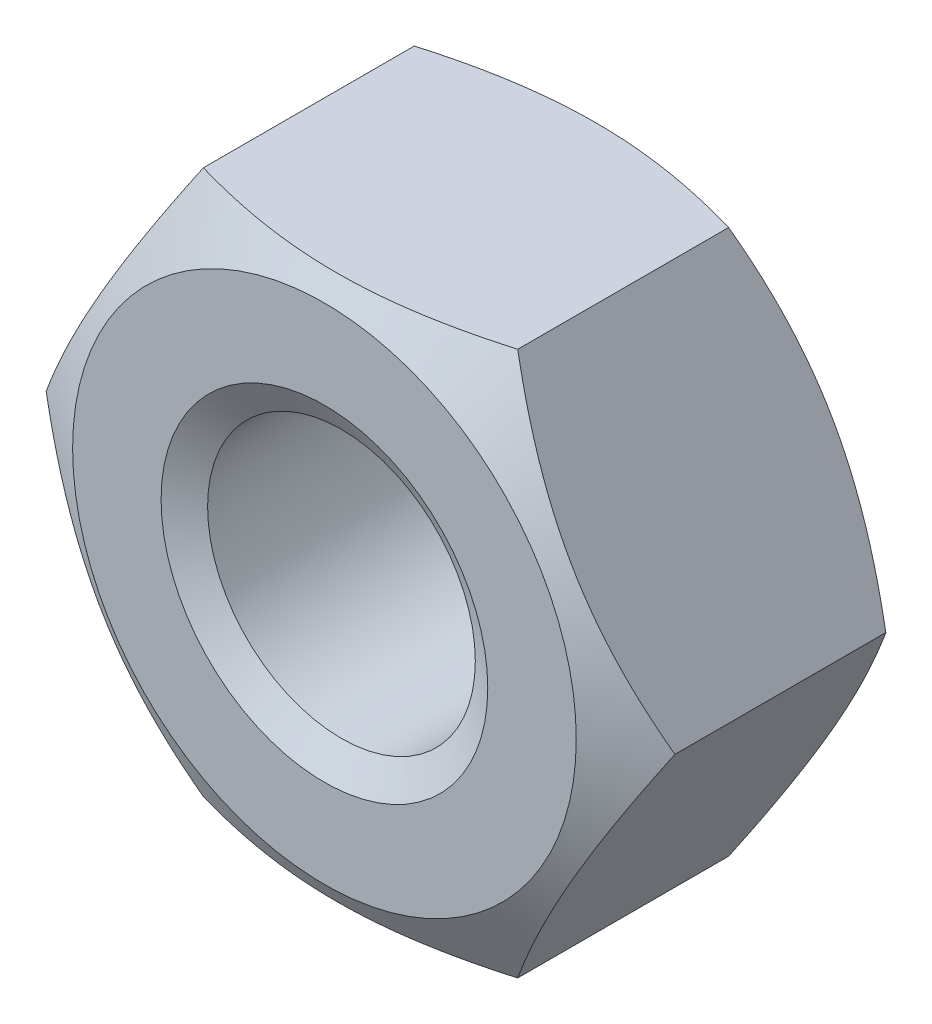
SolidWorks part; units mm, degrees
ref_plane "Front" through (0, 0, 0) normal (0, 0, 1) x (1, 0, 0)
ref_plane "Top" through (0, 0, 0) normal (0, 1, 0) x (1, 0, 0)
ref_plane "Right" through (0, 0, 0) normal (1, 0, 0) x (0, 0, -1)
sketch "Sketch1" plane through (0, 0, 0) normal (0, 0, 1) x (1, 0, 0)
  line L1 (5.7735, 0) -> (2.8868, 5)
  line L2 (2.8868, 5) -> (-2.8868, 5)
  line L3 (-2.8868, 5) -> (-5.7735, 0)
  line L4 (-5.7735, 0) -> (-2.8868, -5)
  line L5 (-2.8868, -5) -> (2.8868, -5)
  line L6 (2.8868, -5) -> (5.7735, 0)
  circle A0 centre (0, 0) radius 5 construction
  circle A1 centre (0, 0) radius 2.4585
  dimension "D" = 4.917
  dimension "s" = 10
extrude "BaseNut" add sketch "Sketch1" against normal blind 5.2
cosmetic thread "ThreadCosmetic1" [suppressed] parameters "D"=6
sketch "Sketch2" plane through (0, 0, 0) normal (0, 1, 0) x (1, 0, 0)
  line L0 (-5.7735, 5.2) -> (-4.625, 5.2)
  line L2 (-4.625, 5.2) -> (-5.7735, 4.5369)
  line L3 (-5.7735, 4.5369) -> (-5.7735, 5.2)
  line L4 (0, 3.3759) -> (0, -9.8171) construction
  line L6 (-9.7712, 2.6) -> (9.8853, 2.6) construction
  line L7 (-5.7735, 0.6631) -> (-5.7735, 0)
  line L8 (-4.625, 0) -> (-5.7735, 0.6631)
  line L9 (-5.7735, 0) -> (-4.625, 0)
  dimension "D1" = 30
  dimension "dw" = 9.25
  dimension "D2" = 2.6
revolve "Double-Chamfer" cut sketch "Sketch2" angle 360 about L4
chamfer "EndChamfer" distance 0.5415 angle 30 2 edges at (2.4585, 0, -5.2) (2.4585, 0, 0)
sketch "Sketch3" plane through (0, 0, 0) normal (0, 1, 0) x (1, 0, 0)
  line L0 (-2.9275, 4.6585) -> (-2.4585, 4.3877)
  line L1 (-2.4585, 4.3877) -> (-1.917, 4.3877)
  line L2 (-1.917, 4.3877) -> (-1.917, 4.9292)
  line L3 (-1.917, 4.9292) -> (-2.4585, 4.9292)
  line L4 (-2.4585, 4.9292) -> (-2.9275, 4.6585)
  line L5 (0, 7.4383) -> (0, 16.8806) construction
  dimension "D1" = 0.5415
  dimension "D2" = 4.917
revolve "Cut-Revolve10" [suppressed] cut sketch "Sketch3" angle 360 about L5
pattern_linear "LPattern10" [suppressed] count 8 spacing 0.6498 along (0, 0, -1)
equation "\"dw@Sketch2\" = \"s@Sketch1\"-0.75"
equation "\"D2@Sketch2\" = \"m@BaseNut\" / 2"
equation "\"D2@Sketch3\" = \"D@Sketch1\""
equation "\"D1@Sketch3\" =  (\"D@ThreadCosmetic1\"   - \"D@Sketch1\")  / 2"
equation "\"D3@LPattern10\" = \"D1@Sketch3\" * 1.2"
equation "\"D1@LPattern10\" = \"m@BaseNut\"/\"D3@LPattern10\""
